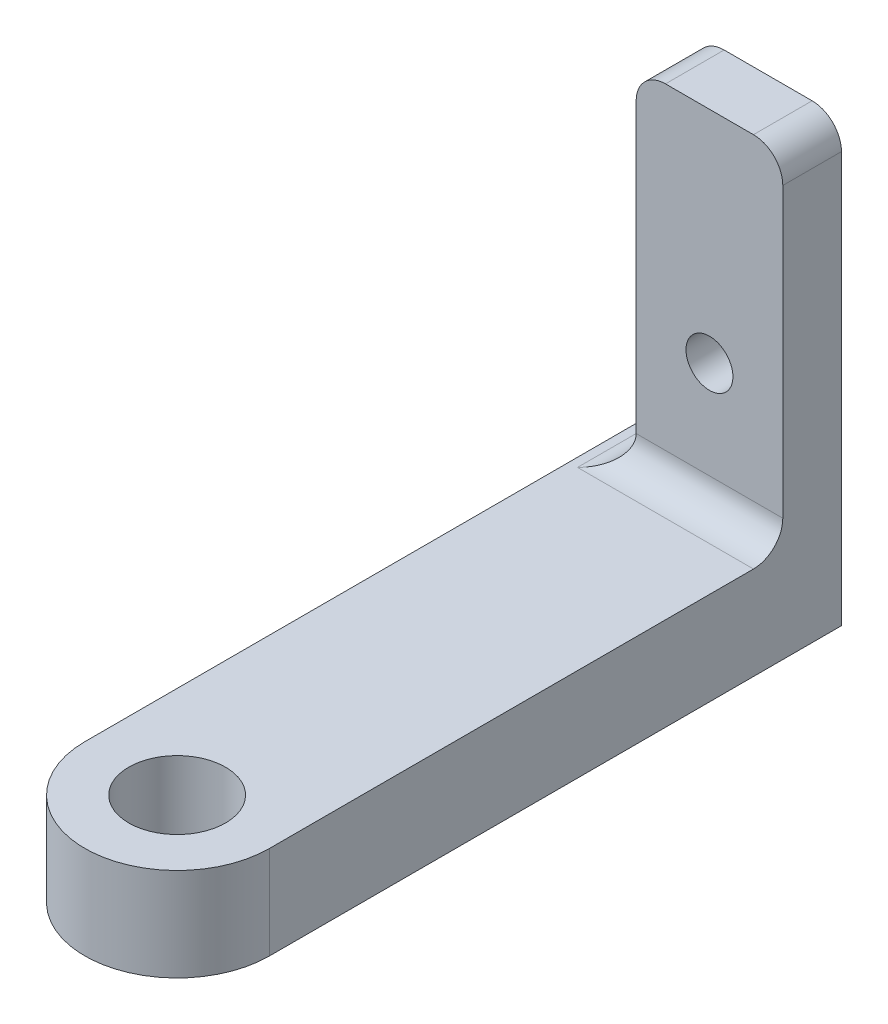
SolidWorks part; units mm, degrees
ref_plane "Front Plane" through (0, 0, 0) normal (0, 0, 1) x (1, 0, 0)
ref_plane "Top Plane" through (0, 0, 0) normal (0, 1, 0) x (1, 0, 0)
ref_plane "Right Plane" through (0, 0, 0) normal (1, 0, 0) x (0, 0, -1)
sketch "Sketch1" plane through (0, 0, 0) normal (0, 1, 0) x (1, 0, 0)
  line L0 (-6.3, 0) -> (-6.3, 39)
  line L1 (-6.3, 39) -> (6.3, 39)
  line L2 (6.3, 39) -> (6.3, 0)
  circle A0 centre (0, 0) radius 3.3
  circle A1 centre (0, 0) radius 6.3
  dimension "D1" = 6.6
  dimension "D3" = 39
  dimension "D2" = 3
extrude "Boss-Extrude1" add sketch "Sketch1" along normal blind 6.35 contours A1 A0 | A1 L2 L1 L0
sketch "Sketch2" plane through (0, 0, -39) normal (0, 0, -1) x (-1, 0, 0)
  line L0 (-6.3, 0) -> (-6.3, 30)
  line L1 (-6.3, 30) -> (3.7, 30)
  line L2 (3.7, 30) -> (3.7, 0)
  line L3 (3.7, 0) -> (-6.3, 0)
  circle A0 centre (-1.3, 15) radius 1.6
  point P8 (3.7, 15)
  point P9 (0, 0)
  point P10 (-1.3, 30)
  dimension "D2" = 3.2
  dimension "D1" = 30
  dimension "D3" = 10
extrude "Boss-Extrude2" add sketch "Sketch2" against normal blind 4
fillet "Fillet1" radius 2 4 edges at (1.3, 6.35, -35) (6.3, 30, -37) (-3.7, 30, -37) (-3.7, 6.35, -37)
